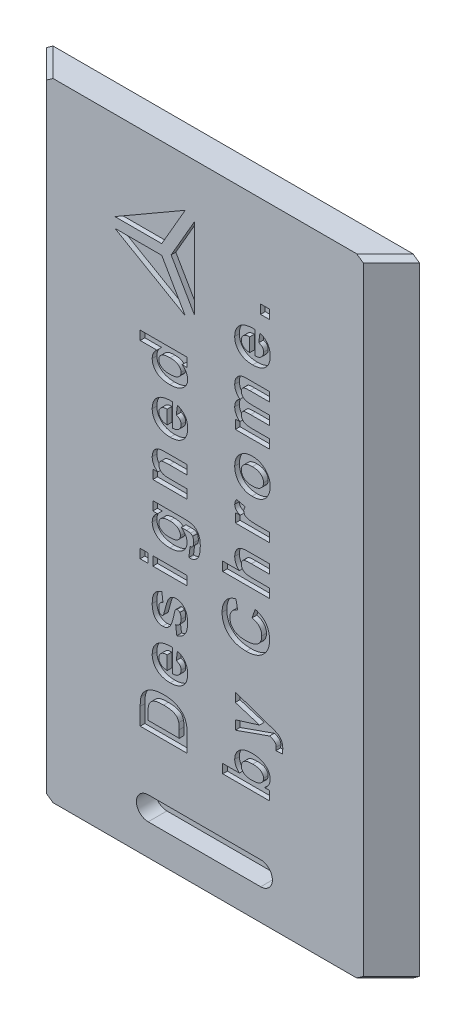
SolidWorks part; units mm, degrees
material "Custom Plastic"
ref_plane "Front Plane" through (0, 0, 0) normal (0, 0, 1) x (1, 0, 0)
ref_plane "Top Plane" through (0, 0, 0) normal (0, 1, 0) x (1, 0, 0)
ref_plane "Right Plane" through (0, 0, 0) normal (1, 0, 0) x (0, 0, -1)
sketch "Sketch1" plane through (0, 0, 0) normal (0, 0, 1) x (1, 0, 0)
  line L1 (0, 0) -> (39.8, 0)
  line L2 (0, 0) -> (0, 66.9)
  line L3 (0, 66.9) -> (39.8, 66.9)
  line L4 (39.8, 0) -> (39.8, 66.9)
  dimension "D1" = 39.8
  dimension "D2" = 66.9
extrude "Boss-Extrude1" add sketch "Sketch1" along normal blind 3
sketch "Sketch2" plane through (0, 0, 0) normal (0, -1, 0) x (1, 0, 0)
  line L0 (0, 0) -> (0, 3)
  line L1 (0, 3) -> (3, 3)
  line L2 (0, 3) -> (39.8, 3) construction
  line L3 (3, 3) -> (0, 0)
  line L4 (39.8, 0) -> (39.8, 3)
  line L5 (39.8, 3) -> (36.8, 3)
  line L6 (36.8, 3) -> (39.8, 0)
  dimension "D1" = 135
  dimension "D2" = 135
extrude "Cut-Extrude2" cut sketch "Sketch2" against normal blind 68
sketch "Sketch3" plane through (0, 0, 3) normal (0, 0, 1) x (1, 0, 0)
  line L0 (18, 62.6863) -> (18, 11.2021) construction
  line L1 (26.8, 62.6863) -> (26.8, 11.2021) construction
  line L2 (3, 66.9) -> (3, 0) construction
  line L3 (36.8, 66.9) -> (36.8, 0) construction
  line L4 (13, 0) -> (13, 66.9) construction
  line L5 (3, 0) -> (36.8, 0) construction
  line L6 (36.8, 66.9) -> (3, 66.9) construction
  line L7 (36.8, 56.9) -> (26.663, 56.9) construction
  line L8 (16.3, 56.9) -> (18.8, 61.2301)
  line L9 (18.8, 61.2301) -> (18.8, 52.5699)
  line L10 (18.8, 52.5699) -> (16.3, 56.9)
  line L11 (10.3, 57.44) -> (15.3, 57.44)
  line L12 (15.3, 57.44) -> (17.8, 61.7701)
  line L13 (17.8, 61.7701) -> (10.3, 57.44)
  line L14 (10.3, 56.36) -> (15.3, 56.36)
  line L15 (15.3, 56.36) -> (17.8, 52.0299)
  line L16 (17.8, 52.0299) -> (10.3, 56.36)
  line L17 (18.8, 47.3611) -> (18.8, 62.4343) construction
  text T0 "Designed" font "Arial" height 5
  text T1 "by Chrome." font "Arial" height 5
  point P11 (18.8, 56.9)
  dimension "D1" = 10
  dimension "D2" = 15
  dimension "D3" = 10
  dimension "D4" = 10
  dimension "D5" = 30
  dimension "D6" = 1
  dimension "D7" = 2.5
  dimension "D8" = 0.54
  dimension "D9" = 1
  dimension "D10" = 5
  dimension "D11" = 0.54
  dimension "D12" = 18
  dimension "D13" = 5
  dimension "D14" = 5
  dimension "D15" = 5
  dimension "D16" = 5
extrude "Cut-Extrude3" cut sketch "Sketch3" against normal blind 0.5
sketch "Sketch4" plane through (0, 0, 3) normal (0, 0, 1) x (1, 0, 0)
  line L1 (13.85, 5.8071) -> (25.85, 5.8071)
  line L3 (13.85, 3.3071) -> (25.85, 3.3071)
  arc A0 (13.85, 3.3071) -> (13.85, 5.8071) centre (13.85, 4.5571) cw
  arc A1 (25.85, 5.8071) -> (25.85, 3.3071) centre (25.85, 4.5571) cw
  dimension "D1" = 2.5
  dimension "D2" = 12
extrude "Cut-Extrude4" cut sketch "Sketch4" against normal blind 2
chamfer "Chamfer3" distance 0.5 angle 45 2 edges at (38.3, 66.9, 1.5) (1.5, 66.9, 1.5)
chamfer "Chamfer4" distance 0.5 angle 45 2 edges at (38.3, 0, 1.5) (1.5, 0, 1.5)
